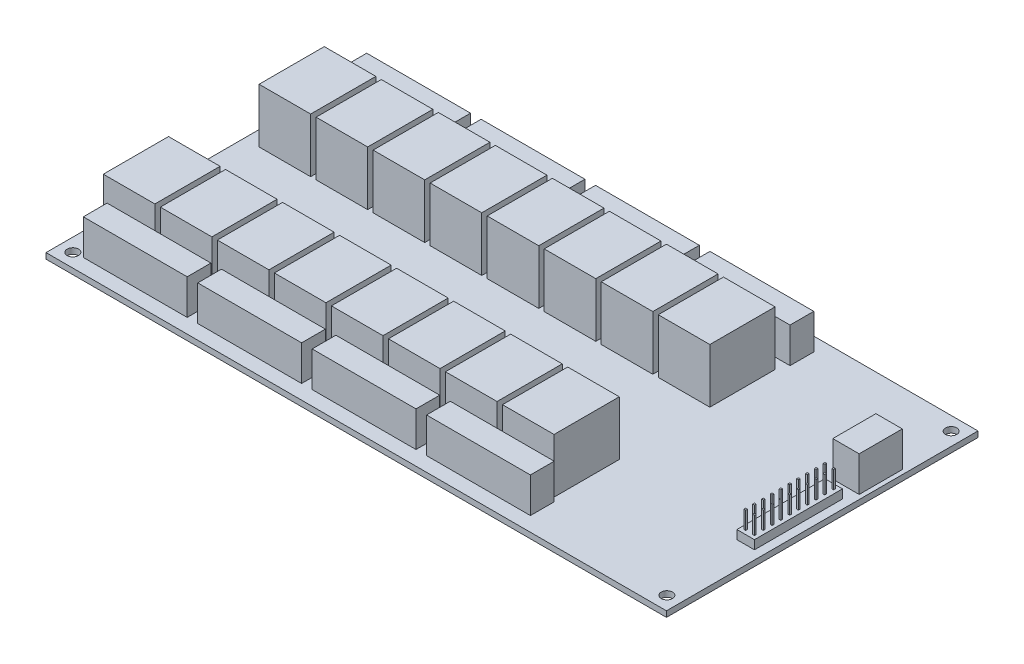
SolidWorks part; units mm, degrees
ref_plane "Front Plane" through (0, 0, 0) normal (0, 0, 1) x (1, 0, 0)
ref_plane "Top Plane" through (0, 0, 0) normal (0, 1, 0) x (1, 0, 0)
ref_plane "Right Plane" through (0, 0, 0) normal (1, 0, 0) x (0, 0, -1)
sketch "Sketch1" plane through (0, 0, 0) normal (0, 1, 0) x (1, 0, 0)
  line L1 (89.535, -44.958) -> (-89.535, -44.958)
  line L2 (89.535, -44.958) -> (89.535, 44.958)
  line L3 (89.535, 44.958) -> (-89.535, 44.958)
  line L4 (-89.535, -44.958) -> (-89.535, 44.958)
  line L5 (89.535, -44.958) -> (-89.535, 44.958) construction
  line L6 (89.535, 44.958) -> (-89.535, -44.958) construction
  point P0 (0, 0)
  dimension "D1" = 89.916
  dimension "D2" = 179.07
extrude "Boss-Extrude1" add sketch "Sketch1" along normal blind 1.651
sketch "Sketch2" plane through (0, 1.651, 0) normal (0, 1, 0) x (1, 0, 0)
  line L1 (85.725, -41.021) -> (-85.725, -41.021) construction
  line L2 (85.725, -41.021) -> (85.725, 41.021) construction
  line L3 (85.725, 41.021) -> (-85.725, 41.021) construction
  line L4 (-85.725, -41.021) -> (-85.725, 41.021) construction
  line L5 (85.725, -41.021) -> (-85.725, 41.021) construction
  line L6 (85.725, 41.021) -> (-85.725, -41.021) construction
  point P0 (0, 0)
  point P6 (-85.725, 41.021)
  point P8 (-85.725, -41.021)
  point P9 (85.725, -41.021)
  point P10 (85.725, 41.021)
  dimension "D1" = 82.042
  dimension "D2" = 171.45
hole_wizard "#30 (0.1285) Diameter Hole1" positions "3DSketch1" profile "Sketch3" hole size "#30" standard "ANSI Inch" end condition through all
sketch3d "3DSketch1"
  point P0 (-85.725, 1.651, 41.021)
  point P3 (-85.725, 1.651, -41.021)
  point P6 (85.725, 1.651, -41.021)
  point P9 (85.725, 1.651, 41.021)
sketch "Sketch3" plane through (-85.725, 1.651, 41.021) normal (1, 0, 0) x (0, 0, 1)
  line L0 (0, 0) -> (0, 1.651)
  line L1 (0, 1.651) -> (1.6319, 1.651)
  line L2 (1.6319, 1.651) -> (1.6319, 0)
  line L5 (1.6319, 0) -> (0, 0)
  line L11 (0, -6.35) -> (0, 107.95) construction
  dimension "Thru Hole Dia." = 3.2639
  dimension "Thru Hole Depth" = 1.651
sketch "Sketch4" plane through (0, 1.651, 0) normal (0, 1, 0) x (1, 0, 0)
  line L0 (-89.535, 44.958) -> (-89.535, -44.958) construction
  line L1 (-85.1916, -32.766) -> (-70.3072, -32.766)
  line L2 (-85.1916, -32.766) -> (-85.1916, -13.9446)
  line L3 (-85.1916, -13.9446) -> (-70.3072, -13.9446)
  line L4 (-70.3072, -32.766) -> (-70.3072, -13.9446)
  line L5 (-89.535, -44.958) -> (89.535, -44.958) construction
  dimension "D1" = 18.8214
  dimension "D2" = 14.8844
  dimension "D3" = 4.3434
  dimension "D4" = 12.192
extrude "Boss-Extrude2" add sketch "Sketch4" along normal blind 15.6718
pattern_linear "LPattern1" count 8 spacing 16.4592 along (1, 0, 0) count 2 spacing 44.958 along (0, 0, -1) of "Boss-Extrude2"
sketch "Sketch5" plane through (0, 1.651, 0) normal (0, 1, 0) x (1, 0, 0)
  line L0 (-89.535, 44.958) -> (-89.535, -44.958) construction
  line L1 (-82.931, -33.9344) -> (-52.959, -33.9344)
  line L2 (-82.931, -33.9344) -> (-82.931, -40.7924)
  line L3 (-82.931, -40.7924) -> (-52.959, -40.7924)
  line L4 (-52.959, -33.9344) -> (-52.959, -40.7924)
  line L5 (-89.535, -44.958) -> (89.535, -44.958) construction
  point P4 (-82.931, -37.3634)
  dimension "D1" = 29.972
  dimension "D2" = 6.858
  dimension "D3" = 6.604
  dimension "D4" = 4.1656
extrude "Boss-Extrude3" add sketch "Sketch5" along normal blind 10.16
pattern_linear "LPattern2" count 4 spacing 33.02 along (1, 0, 0) count 2 spacing 74.93 along (0, 0, -1) of "Boss-Extrude3"
sketch "Sketch6" plane through (0, 1.651, 0) normal (0, 1, 0) x (1, 0, 0)
  line L0 (89.535, 44.958) -> (-89.535, 44.958) construction
  line L1 (80.645, 24.384) -> (88.265, 24.384)
  line L2 (80.645, 24.384) -> (80.645, 11.9311)
  line L3 (80.645, 11.9311) -> (88.265, 11.9311)
  line L4 (88.265, 24.384) -> (88.265, 11.9311)
  line L5 (89.535, -44.958) -> (89.535, 44.958) construction
  dimension "D1" = 20.574
  dimension "D2" = 1.27
  dimension "D3" = 7.62
extrude "Boss-Extrude4" add sketch "Sketch6" along normal blind 10.16
sketch "Sketch7" plane through (0, 1.651, 0) normal (0, 1, 0) x (1, 0, 0)
  line L0 (-89.535, -44.958) -> (89.535, -44.958) construction
  line L1 (81.915, 8.382) -> (86.995, 8.382)
  line L2 (81.915, 8.382) -> (81.915, -17.018)
  line L3 (81.915, -17.018) -> (86.995, -17.018)
  line L4 (86.995, 8.382) -> (86.995, -17.018)
  line L5 (89.535, -44.958) -> (89.535, 44.958) construction
  dimension "D1" = 5.08
  dimension "D2" = 25.4
  dimension "D3" = 27.94
  dimension "D4" = 2.54
extrude "Boss-Extrude5" add sketch "Sketch7" along normal blind 2.54
sketch "Sketch8" plane through (0, 4.191, 0) normal (0, 1, 0) x (1, 0, 0)
  line L1 (85.471, 7.366) -> (85.979, 7.366)
  line L2 (85.471, 7.366) -> (85.471, 6.858)
  line L3 (85.471, 6.858) -> (85.979, 6.858)
  line L4 (85.979, 7.366) -> (85.979, 6.858)
  line L5 (86.995, -17.018) -> (86.995, 8.382) construction
  line L6 (86.995, 8.382) -> (81.915, 8.382) construction
  point P8 (85.725, 7.366)
  point P9 (85.979, 7.112)
  dimension "D1" = 0.508
  dimension "D2" = 1.27
  dimension "D3" = 1.27
extrude "Boss-Extrude6" add sketch "Sketch8" along normal blind 5.08
pattern_linear "LPattern3" count 10 spacing 2.54 along (0, 0, 1) count 2 spacing 2.54 along (-1, 0, 0) of "Boss-Extrude6"
